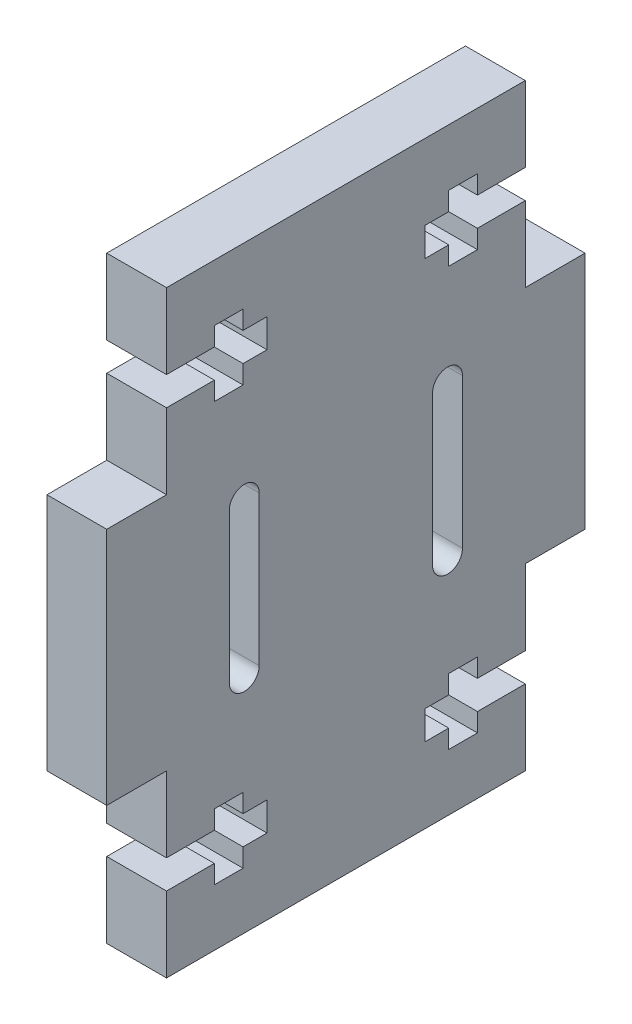
SolidWorks part; units mm, degrees
material "Acrylic (Medium-high impact)"
ref_plane "Front Plane" through (0, 0, 0) normal (0, 0, 1) x (1, 0, 0)
ref_plane "Top Plane" through (0, 0, 0) normal (0, 1, 0) x (1, 0, 0)
ref_plane "Right Plane" through (0, 0, 0) normal (1, 0, 0) x (0, 0, -1)
sketch "Sketch1" plane through (0, 0, 0) normal (1, 0, 0) x (0, 0, -1)
  line L0 (0, 0) -> (0, 50) construction
  line L1 (-15, 50) -> (15, 50)
  line L2 (15, 50) -> (15, 35)
  line L3 (15, 35) -> (20, 35)
  line L4 (20, 35) -> (20, 15)
  line L5 (20, 15) -> (15, 15)
  line L6 (15, 15) -> (15, 0)
  line L7 (15, 0) -> (-15, 0)
  line L8 (-15, 15) -> (-15, 0)
  line L9 (-20, 15) -> (-15, 15)
  line L10 (-20, 35) -> (-20, 15)
  line L11 (-15, 35) -> (-20, 35)
  line L12 (-15, 50) -> (-15, 35)
  line L13 (8.5, 31.25) -> (8.5, 18.75) construction
  line L14 (9.75, 31.25) -> (9.75, 18.75)
  line L15 (7.25, 31.25) -> (7.25, 18.75)
  line L16 (-8.5, 31.25) -> (-8.5, 18.75) construction
  line L17 (-9.75, 31.25) -> (-9.75, 18.75)
  line L18 (-7.25, 31.25) -> (-7.25, 18.75)
  arc A0 (9.75, 31.25) -> (7.25, 31.25) centre (8.5, 31.25) ccw
  arc A1 (7.25, 18.75) -> (9.75, 18.75) centre (8.5, 18.75) ccw
  arc A2 (-9.75, 31.25) -> (-7.25, 31.25) centre (-8.5, 31.25) cw
  arc A3 (-7.25, 18.75) -> (-9.75, 18.75) centre (-8.5, 18.75) cw
  point P17 (8.5, 25)
  point P24 (-8.5, 25)
  point P29 (0, 25)
  dimension "D7" = 8.5
  dimension "D6" = 1.25
  dimension "D1" = 20
  dimension "D2" = 15
  dimension "D3" = 15
  dimension "D4" = 15
  dimension "D5" = 5
  dimension "D8" = 12.5
  dimension "D9" = 1
extrude "Boss-Extrude1" add sketch "Sketch1" along normal blind 5
sketch "Sketch2" plane through (5, 0, 0) normal (1, 0, 0) x (0, 0, -1)
  line L0 (0, 50) -> (0, 0) construction
  line L1 (15, 50) -> (-15, 50) construction
  line L2 (-15, 0) -> (15, 0) construction
  line L3 (-15, 42.5) -> (15, 42.5) construction
  line L4 (-15, 50) -> (-15, 35) construction
  line L5 (15, 35) -> (15, 50) construction
  line L6 (-15, 43.7) -> (-11, 43.7)
  line L7 (-11, 43.7) -> (-11, 45.25)
  line L8 (-11, 45.25) -> (-8.6, 45.25)
  line L9 (-8.6, 45.25) -> (-8.6, 43.7)
  line L10 (-8.6, 43.7) -> (-6.6, 43.7)
  line L11 (-6.6, 43.7) -> (-6.6, 41.3)
  line L12 (-15, 43.7) -> (-15, 41.3)
  line L13 (-8.6, 41.3) -> (-6.6, 41.3)
  line L14 (-8.6, 39.75) -> (-8.6, 41.3)
  line L15 (-11, 39.75) -> (-8.6, 39.75)
  line L16 (-11, 41.3) -> (-11, 39.75)
  line L17 (-15, 41.3) -> (-11, 41.3)
  line L18 (15, 41.3) -> (11, 41.3)
  line L19 (11, 41.3) -> (11, 39.75)
  line L20 (11, 39.75) -> (8.6, 39.75)
  line L21 (8.6, 39.75) -> (8.6, 41.3)
  line L22 (8.6, 41.3) -> (6.6, 41.3)
  line L23 (15, 43.7) -> (15, 41.3)
  line L24 (6.6, 43.7) -> (6.6, 41.3)
  line L25 (8.6, 43.7) -> (6.6, 43.7)
  line L26 (8.6, 45.25) -> (8.6, 43.7)
  line L27 (11, 45.25) -> (8.6, 45.25)
  line L28 (11, 43.7) -> (11, 45.25)
  line L29 (15, 43.7) -> (11, 43.7)
  line L30 (-15, 8.7) -> (-11, 8.7)
  line L31 (-11, 8.7) -> (-11, 10.25)
  line L32 (-11, 10.25) -> (-8.6, 10.25)
  line L33 (-8.6, 10.25) -> (-8.6, 8.7)
  line L34 (-8.6, 8.7) -> (-6.6, 8.7)
  line L35 (-6.6, 8.7) -> (-6.6, 6.3)
  line L36 (-15, 8.7) -> (-15, 6.3)
  line L37 (-8.6, 6.3) -> (-6.6, 6.3)
  line L38 (-8.6, 4.75) -> (-8.6, 6.3)
  line L39 (-11, 4.75) -> (-8.6, 4.75)
  line L40 (-11, 6.3) -> (-11, 4.75)
  line L41 (-15, 6.3) -> (-11, 6.3)
  line L42 (15, 6.3) -> (11, 6.3)
  line L43 (11, 6.3) -> (11, 4.75)
  line L44 (11, 4.75) -> (8.6, 4.75)
  line L45 (8.6, 4.75) -> (8.6, 6.3)
  line L46 (8.6, 6.3) -> (6.6, 6.3)
  line L47 (15, 8.7) -> (15, 6.3)
  line L48 (6.6, 8.7) -> (6.6, 6.3)
  line L49 (8.6, 8.7) -> (6.6, 8.7)
  line L50 (8.6, 10.25) -> (8.6, 8.7)
  line L51 (11, 10.25) -> (8.6, 10.25)
  line L52 (11, 8.7) -> (11, 10.25)
  line L53 (15, 8.7) -> (11, 8.7)
  line L54 (-15, 7.5) -> (15, 7.5) construction
  point P21 (-6.6, 42.5)
  point P37 (6.6, 42.5)
  point P50 (-6.6, 7.5)
  point P66 (6.6, 7.5)
  dimension "D1" = 2.4
  dimension "D2" = 5.5
  dimension "D3" = 4
  dimension "D4" = 2.4
  dimension "D5" = 2
extrude "Cut-Extrude1" cut sketch "Sketch2" against normal through all
